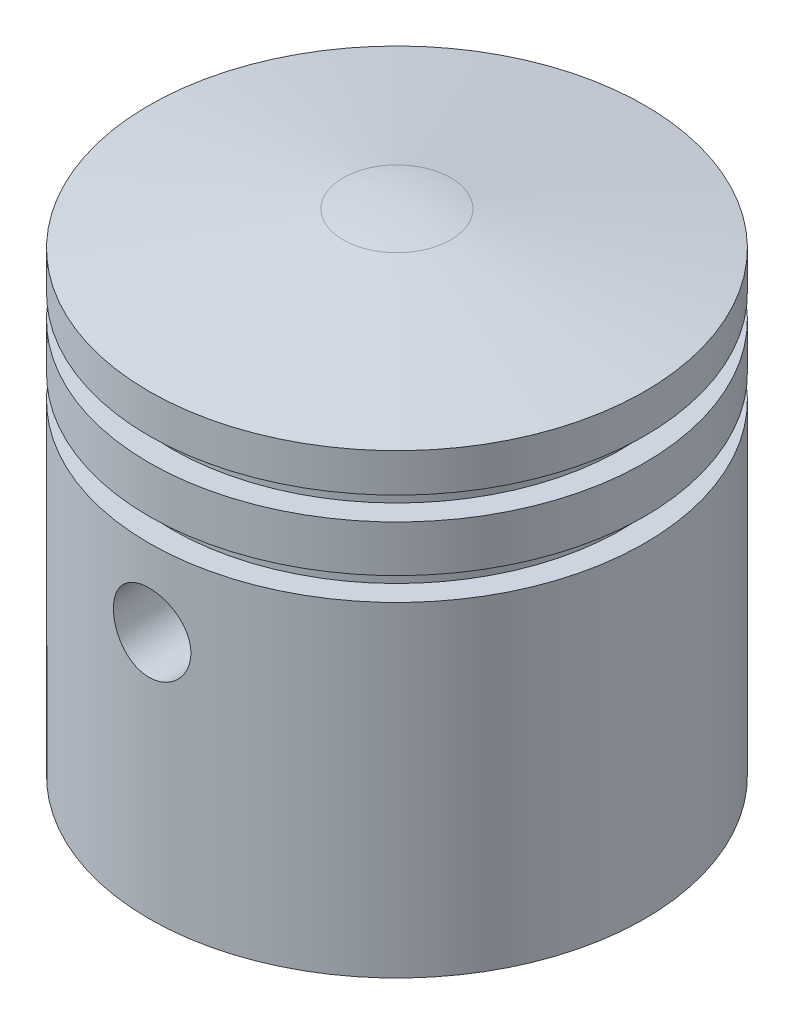
SolidWorks part; units mm, degrees
ref_plane "Front Plane" through (0, 0, 0) normal (0, 0, 1) x (1, 0, 0)
ref_plane "Top Plane" through (0, 0, 0) normal (0, 1, 0) x (1, 0, 0)
ref_plane "Right Plane" through (0, 0, 0) normal (1, 0, 0) x (0, 0, -1)
sketch "Sketch1" plane through (0, 0, 0) normal (0, 0, 1) x (1, 0, 0)
  line L0 (0, 16) -> (0, -16)
  line L2 (16, 13.4873) -> (16, 11)
  line L3 (16, 11) -> (14.5, 11)
  line L4 (14.5, 11) -> (14.5, 9.5)
  line L5 (14.5, 9.5) -> (16, 9.5)
  line L6 (16, 9.5) -> (16, 6.5)
  line L7 (16, 6.5) -> (14.5, 6.5)
  line L8 (14.5, 6.5) -> (14.5, 5)
  line L9 (14.5, 5) -> (16, 5)
  line L10 (16, 5) -> (16, -16)
  line L11 (16, -16) -> (0, -16)
  line L12 (3.473, 15.6962) -> (16, 13.4873)
  line L13 (0, 16) -> (19.1584, 16) construction
  arc A0 (0, 16) -> (3.473, 15.6962) centre (0, -4) cw
  point P4 (0, 0)
  point P6 (14.5, 10.25)
  dimension "D6" = 20
  dimension "D1" = 32
  dimension "D2" = 1.5
  dimension "D3" = 14.5
  dimension "D4" = 3
  dimension "D5" = 21
  dimension "D7" = 1.5
  dimension "D8" = 10
revolve "Revolve1" add sketch "Sketch1" angle 360 about L0
sketch "Sketch2" plane through (0, 0, 0) normal (0, 0, 1) x (1, 0, 0)
  line L0 (-16, -16) -> (16, -16) construction
  circle A0 centre (0, 0) radius 2.5
  dimension "D2" = 5
  dimension "D1" = 16
extrude "Cut-Extrude1" cut sketch "Sketch2" against normal through all both and the other way through all
sketch "Sketch3" plane through (0, -16, 0) normal (0, -1, 0) x (1, 0, 0)
  circle A0 centre (0, 0) radius 10
  dimension "D1" = 20
extrude "Cut-Extrude2" cut sketch "Sketch3" against normal blind 24
sketch "Sketch4" plane through (0, -16, 0) normal (0, -1, 0) x (1, 0, 0)
  circle A0 centre (0, 0) radius 13
  dimension "D1" = 26
extrude "Cut-Extrude3" cut sketch "Sketch4" against normal blind 10
